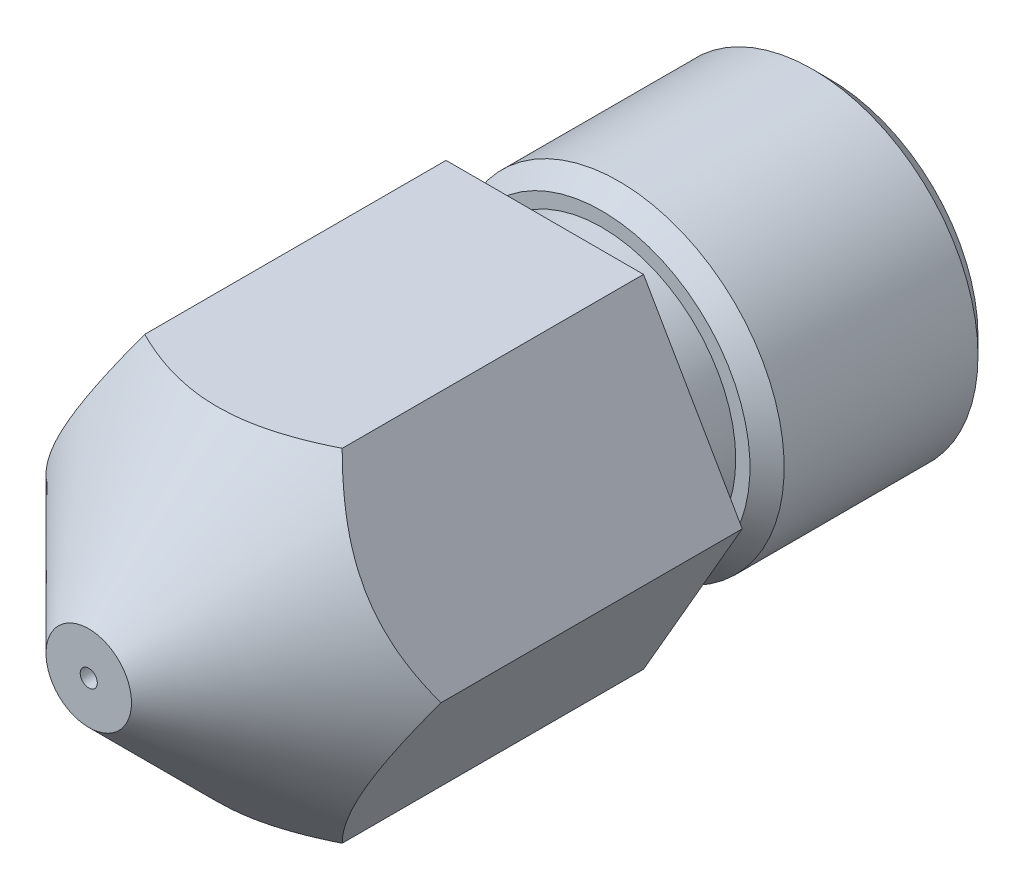
SolidWorks part; units mm, degrees
ref_plane "Спереди" through (0, 0, 0) normal (0, 0, 1) x (1, 0, 0)
ref_plane "Сверху" through (0, 0, 0) normal (0, 1, 0) x (1, 0, 0)
ref_plane "Справа" through (0, 0, 0) normal (1, 0, 0) x (0, 0, -1)
sketch "Эскиз1" plane through (0, 0, 0) normal (0, 0, 1) x (1, 0, 0)
  line L1 (3.4641, 0) -> (1.7321, 3)
  line L2 (1.7321, 3) -> (-1.7321, 3)
  line L3 (-1.7321, 3) -> (-3.4641, 0)
  line L4 (-3.4641, 0) -> (-1.7321, -3)
  line L5 (-1.7321, -3) -> (1.7321, -3)
  line L6 (1.7321, -3) -> (3.4641, 0)
  circle A0 centre (0, 0) radius 3 construction
extrude "Бобышка-Вытянуть1" add sketch "Эскиз1" along normal blind 13
sketch "Эскиз2" plane through (0, 0, 13) normal (0, 0, 1) x (1, 0, 0)
  circle A0 centre (0, 0) radius 0.75
extrude "Вырез-Вытянуть1" cut sketch "Эскиз2" against normal blind 13 draft 45 flip side to cut
sketch "Эскиз3" plane through (0, 0, 0) normal (0, 0, -1) x (-1, 0, 0)
  circle A0 centre (0, 0) radius 2.35
extrude "Вырез-Вытянуть2" cut sketch "Эскиз3" against normal blind 5 flip side to cut
sketch "Эскиз4" plane through (0, 0, 0) normal (0, 0, -1) x (-1, 0, 0)
  circle A0 centre (0, 0) radius 1
extrude "Вырез-Вытянуть3" cut sketch "Эскиз4" against normal blind 12
sketch "Эскиз5" plane through (0, 0, 13) normal (0, 0, 1) x (1, 0, 0)
  circle A0 centre (0, 0) radius 0.15
extrude "Вырез-Вытянуть4" cut sketch "Эскиз5" against normal blind 1
sketch "Эскиз6" plane through (0, 0, 0) normal (0, 0, -1) x (-1, 0, 0)
  circle A0 centre (0, 0) radius 2.35
  circle A1 centre (0, 0) radius 2.9
extrude "Бобышка-Вытянуть2" add sketch "Эскиз6" against normal blind 4
chamfer "Фаска1" distance 0.3 angle 45 3 edges at (-1, 0, 0) (-2.9, 0, 4) (-2.9, 0, 0)
